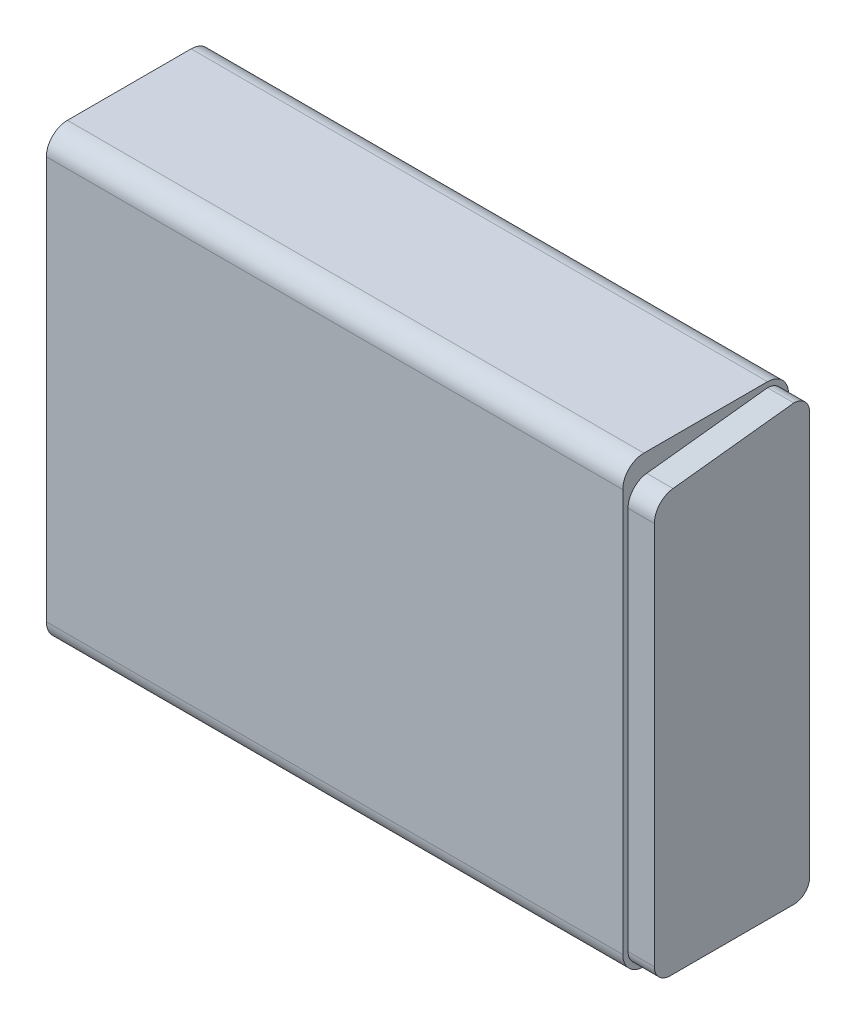
SolidWorks part; units mm, degrees
ref_plane "Front Plane" through (0, 0, 0) normal (0, 0, 1) x (1, 0, 0)
ref_plane "Top Plane" through (0, 0, 0) normal (0, 1, 0) x (1, 0, 0)
ref_plane "Right Plane" through (0, 0, 0) normal (1, 0, 0) x (0, 0, -1)
sketch "Sketch1" plane through (0, 0, 0) normal (1, 0, 0) x (0, 0, -1)
  line L1 (12.7, 0) -> (87.3125, 0)
  line L2 (0, 12.7) -> (0, 255.5875)
  line L3 (12.7, 268.2875) -> (87.3125, 268.2875)
  line L4 (100.0125, 12.7) -> (100.0125, 255.5875)
  arc A0 (12.7, 268.2875) -> (0, 255.5875) centre (12.7, 255.5875) ccw
  arc A1 (100.0125, 12.7) -> (87.3125, 0) centre (87.3125, 12.7) cw
  arc A2 (100.0125, 255.5875) -> (87.3125, 268.2875) centre (87.3125, 255.5875) ccw
  arc A3 (0, 12.7) -> (12.7, 0) centre (12.7, 12.7) ccw
  point P13 (0, 0)
  dimension "D1" = 12.7
  dimension "D2" = 12.7
  dimension "D3" = 12.7
extrude "Boss-Extrude1" add sketch "Sketch1" against normal blind 347.6625
sketch "Sketch2" plane through (0, 0, 0) normal (1, 0, 0) x (0, 0, -1)
  line L5 (14.4464, 256.8635) -> (87.3125, 265.1125)
  line L9 (3.175, 244.2441) -> (3.175, 12.7)
  line L10 (12.7, 3.175) -> (87.3125, 3.175)
  line L11 (96.8375, 12.7) -> (96.8375, 255.5875)
  arc A0 (3.175, 244.2441) -> (14.4464, 256.8635) centre (15.875, 244.2441) cw
  arc A9 (3.175, 12.7) -> (12.7, 3.175) centre (12.7, 12.7) ccw
  arc A10 (87.3125, 3.175) -> (96.8375, 12.7) centre (87.3125, 12.7) ccw
  arc A11 (96.8375, 255.5875) -> (87.3125, 265.1125) centre (87.3125, 255.5875) ccw
  dimension "D1" = 12.7
extrude "Boss-Extrude2" add sketch "Sketch2" along normal blind 15.875
